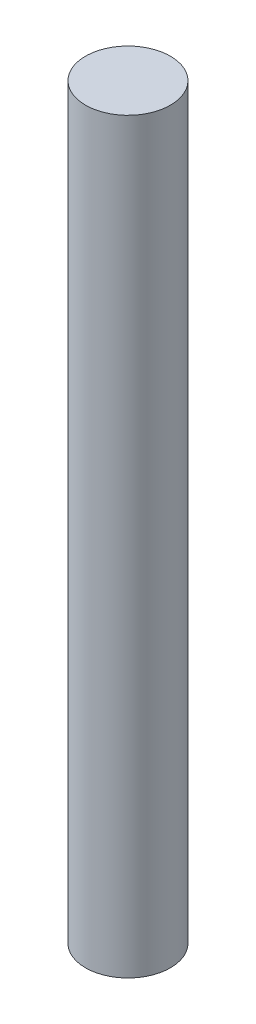
SolidWorks part; units mm, degrees
ref_plane "Front Plane" through (0, 0, 0) normal (0, 0, 1) x (1, 0, 0)
ref_plane "Top Plane" through (0, 0, 0) normal (0, 1, 0) x (1, 0, 0)
ref_plane "Right Plane" through (0, 0, 0) normal (1, 0, 0) x (0, 0, -1)
sketch "Sketch1" plane through (0, 0, 0) normal (0, 1, 0) x (1, 0, 0)
  circle A0 centre (0, 0) radius 15.875
  dimension "D1" = 31.75
extrude "Boss-Extrude1" add sketch "Sketch1" along normal blind 279.4
